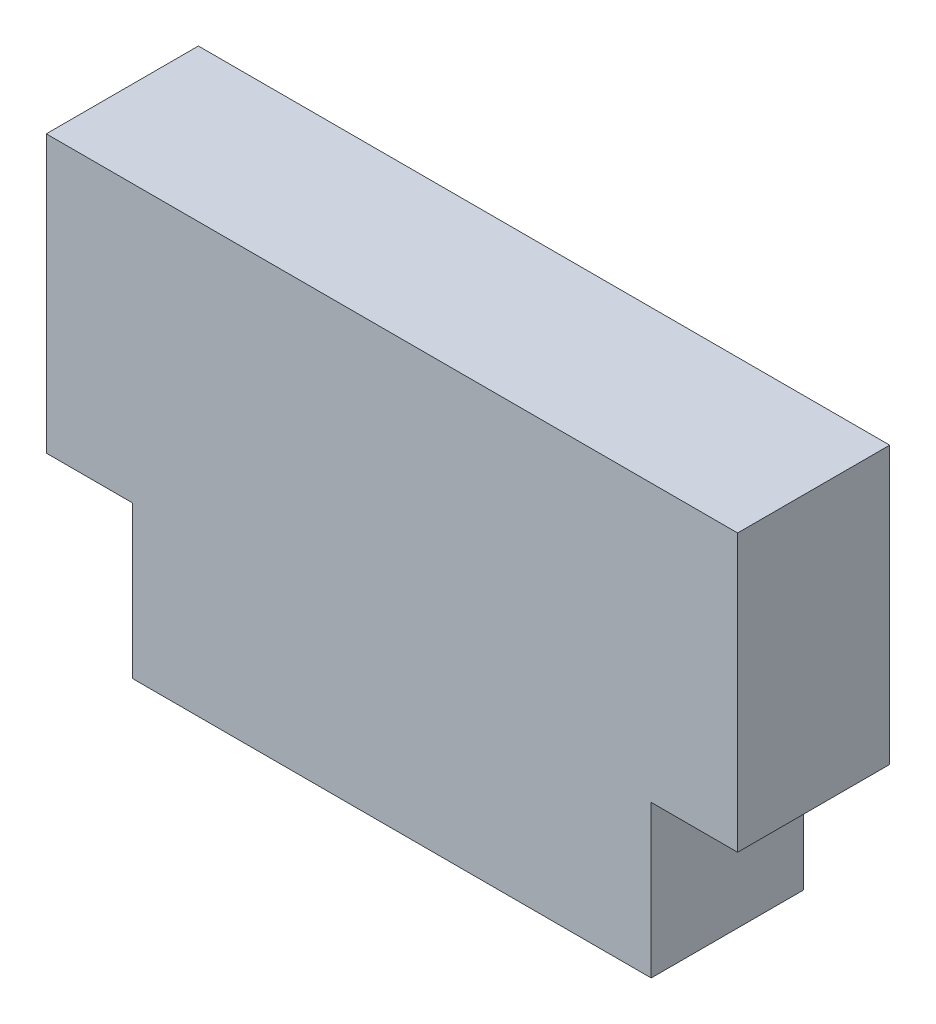
SolidWorks part; units mm, degrees
ref_plane "Front Plane" through (0, 0, 0) normal (0, 0, 1) x (1, 0, 0)
ref_plane "Top Plane" through (0, 0, 0) normal (0, 1, 0) x (1, 0, 0)
ref_plane "Right Plane" through (0, 0, 0) normal (1, 0, 0) x (0, 0, -1)
sketch "Sketch1" plane through (0, 0, 0) normal (0, 0, 1) x (1, 0, 0)
  line L0 (0, 0) -> (0, -7.874) construction
  line L1 (-12.7, -5.08) -> (-9.525, -5.08)
  line L2 (-12.7, -5.08) -> (-12.7, 5.08)
  line L3 (-12.7, 5.08) -> (12.7, 5.08)
  line L4 (12.7, -5.08) -> (12.7, 5.08)
  line L5 (-12.7, -5.08) -> (12.7, 5.08) construction
  line L6 (-12.7, 5.08) -> (12.7, -5.08) construction
  line L7 (9.525, -5.08) -> (12.7, -5.08)
  line L9 (-9.525, -5.08) -> (-9.525, -10.668)
  line L10 (-9.525, -10.668) -> (9.525, -10.668)
  line L11 (9.525, -5.08) -> (9.525, -10.668)
  line L12 (-9.525, -5.08) -> (9.525, -10.668) construction
  line L13 (-9.525, -10.668) -> (9.525, -5.08) construction
  point P0 (0, 0)
  dimension "D1" = 10.16
  dimension "D2" = 25.4
  dimension "D3" = 3.175
  dimension "D4" = 5.588
extrude "Boss-Extrude1" add sketch "Sketch1" along normal blind 5.588
